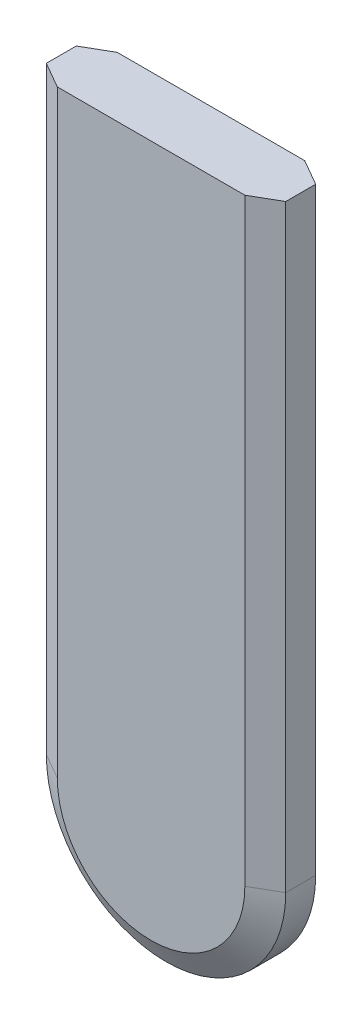
SolidWorks part; units mm, degrees
ref_plane "Front Plane" through (0, 0, 0) normal (0, 0, 1) x (1, 0, 0)
ref_plane "Top Plane" through (0, 0, 0) normal (0, 1, 0) x (1, 0, 0)
ref_plane "Right Plane" through (0, 0, 0) normal (1, 0, 0) x (0, 0, -1)
sketch "Sketch1" plane through (0, 0, 0) normal (0, 0, 1) x (1, 0, 0)
  line L0 (0, 0) -> (0, -63.5)
  line L2 (25.4, -63.5) -> (25.4, 0)
  line L3 (25.4, 0) -> (0, 0)
  arc A0 (0, -63.5) -> (25.4, -63.5) centre (12.7, -63.5) ccw
  dimension "D3" = 12.7
  dimension "D1" = 25.4
  dimension "D2" = 63.5
extrude "Boss-Extrude1" add sketch "Sketch1" along normal blind 6.35
chamfer "Chamfer1" distance 1.5875 angle 60 3 edges at (25.4, -31.75, 6.35) (12.7, -76.2, 6.35) (0, -31.75, 6.35)
chamfer "Chamfer2" distance 1.5875 angle 60 3 edges at (0, -31.75, 0) (12.7, -76.2, 0) (25.4, -31.75, 0)
